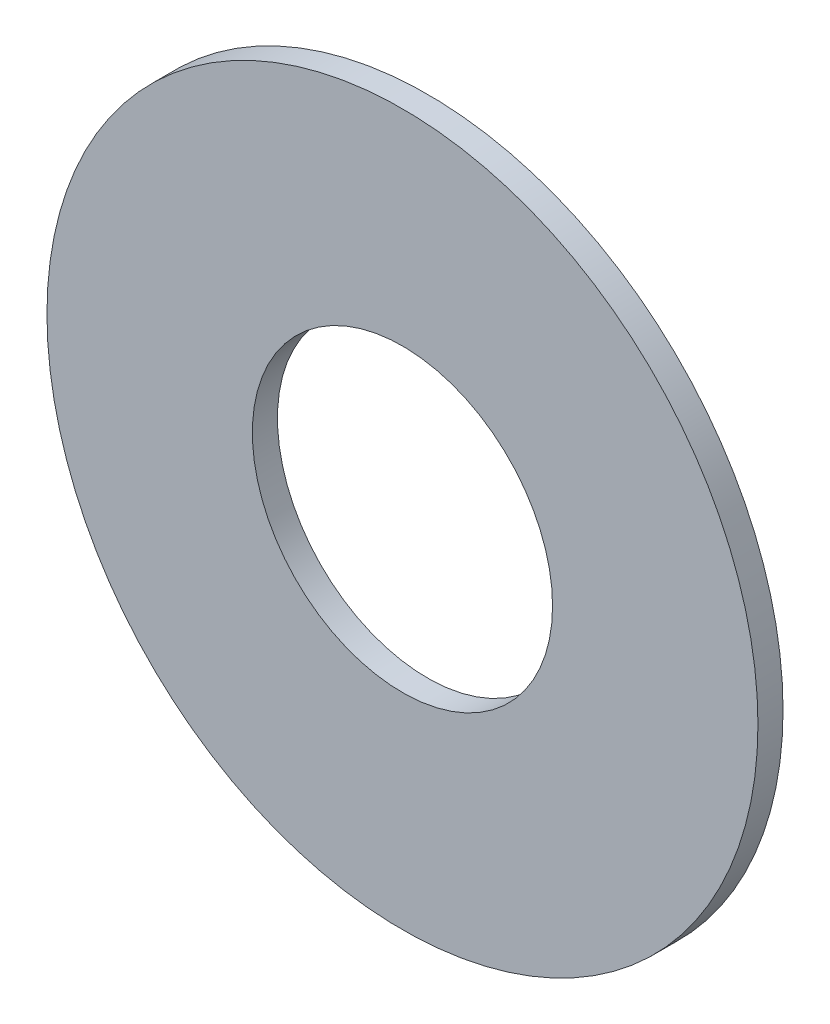
SolidWorks part; units mm, degrees
ref_plane "Front Plane" through (0, 0, 0) normal (0, 0, 1) x (1, 0, 0)
ref_plane "Top Plane" through (0, 0, 0) normal (0, 1, 0) x (1, 0, 0)
ref_plane "Right Plane" through (0, 0, 0) normal (1, 0, 0) x (0, 0, -1)
sketch "Sketch1" plane through (0, 0, 0) normal (0, 0, 1) x (1, 0, 0)
  circle A0 centre (0, 0) radius 11.25
  circle A1 centre (0, 0) radius 4.75
  dimension "D1" = 9.5
  dimension "D2" = 22.5
extrude "Boss-Extrude1" add sketch "Sketch1" along normal blind 0.7937
